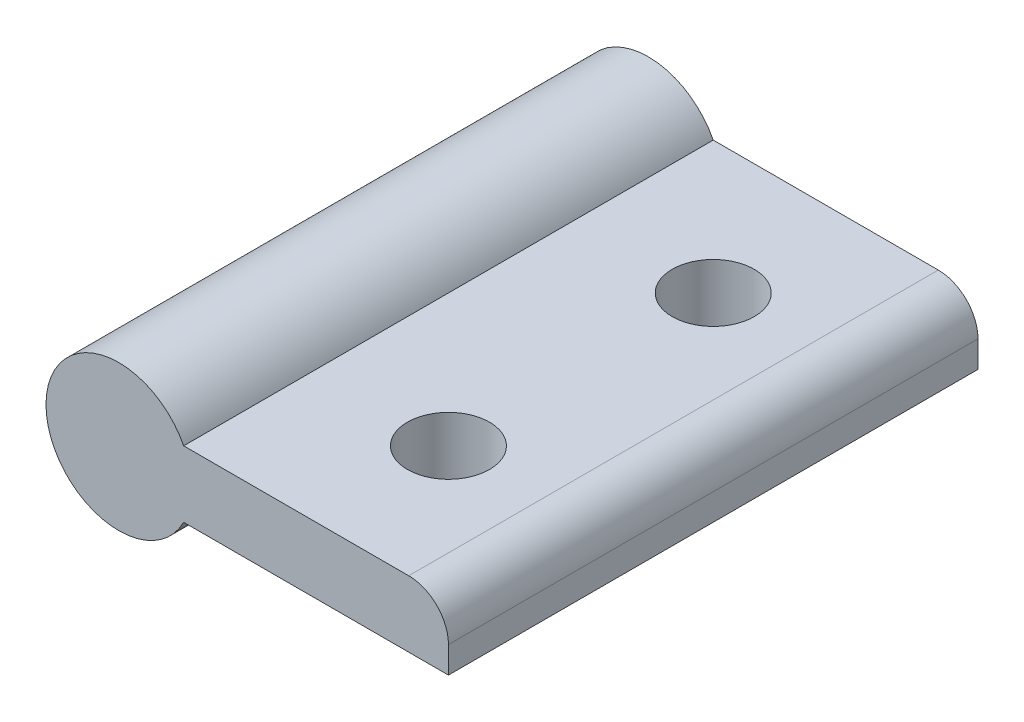
SolidWorks part; units mm, degrees
ref_plane "Front Plane" through (0, 0, 0) normal (0, 0, 1) x (1, 0, 0)
ref_plane "Top Plane" through (0, 0, 0) normal (0, 1, 0) x (1, 0, 0)
ref_plane "Right Plane" through (0, 0, 0) normal (1, 0, 0) x (0, 0, -1)
sketch "Sketch1" plane through (0, 0, 0) normal (0, 0, 1) x (1, 0, 0)
  line L0 (0, 0) -> (32.5662, 0) construction
  line L1 (4.899, 2.5) -> (24.899, 2.5)
  line L2 (4.899, 2.5) -> (4.899, -2.5)
  line L3 (4.899, -2.5) -> (24.899, -2.5)
  line L4 (24.899, 2.5) -> (24.899, -2.5)
  circle A0 centre (0, 0) radius 5.5
  point P7 (24.899, 0)
  dimension "D1" = 11
  dimension "D2" = 5
  dimension "D3" = 20
extrude "Boss-Extrude1" add sketch "Sketch1" along normal blind 40
sketch "Sketch2" plane through (0, 2.5, 0) normal (0, 1, 0) x (1, 0, 0)
  line L0 (14.899, 0) -> (14.899, -40) construction
  line L1 (4.899, 0) -> (24.899, 0) construction
  line L2 (4.899, -40) -> (24.899, -40) construction
  circle A0 centre (14.899, -10) radius 3.1
  circle A1 centre (14.899, -30) radius 3.1
  dimension "D3" = 6.2
  dimension "D4" = 6.2
  dimension "D1" = 10
  dimension "D2" = 10
extrude "Cut-Extrude1" cut sketch "Sketch2" against normal blind 10
fillet "Fillet1" radius 3 1 edges at (24.899, 2.5, 20)
